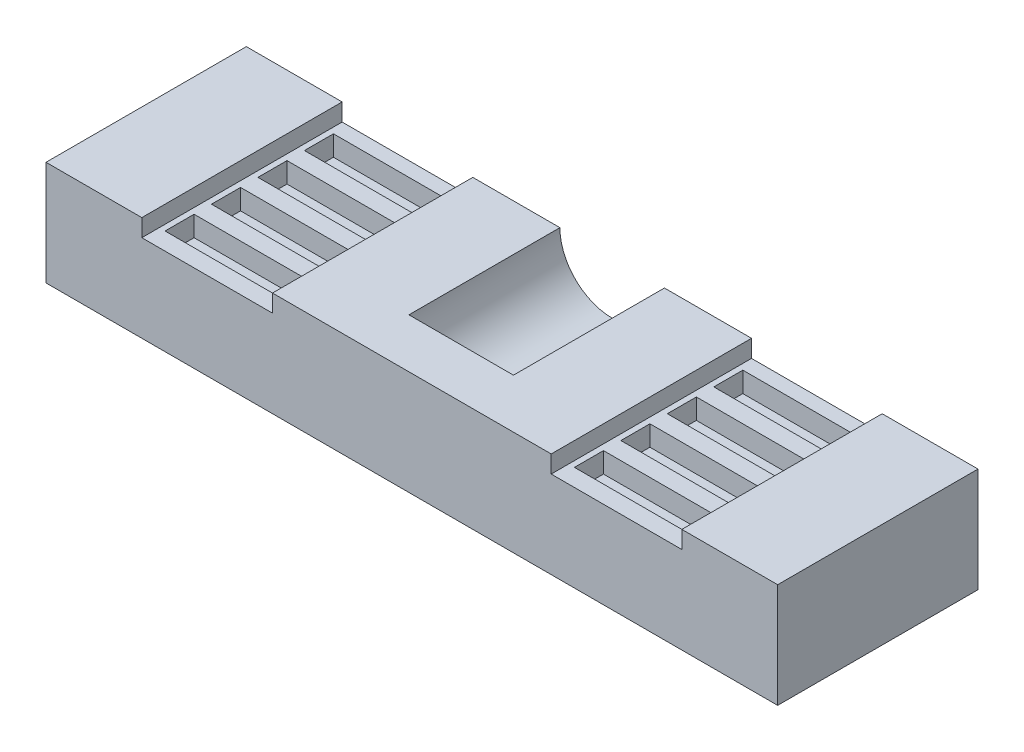
SolidWorks part; units mm, degrees
ref_plane "Alzado" through (0, 0, 0) normal (0, 0, 1) x (1, 0, 0)
ref_plane "Planta" through (0, 0, 0) normal (0, 1, 0) x (1, 0, 0)
ref_plane "Vista lateral" through (0, 0, 0) normal (1, 0, 0) x (0, 0, -1)
sketch "Croquis1" plane through (0, 0, 0) normal (0, 0, 1) x (1, 0, 0)
  line L0 (0, 0) -> (0, 18)
  line L1 (0, 18) -> (16.5, 18)
  line L2 (16.5, 18) -> (16.5, 15)
  line L3 (16.5, 15) -> (39, 15)
  line L4 (39, 15) -> (39, 18)
  line L5 (39, 18) -> (87, 18)
  line L6 (87, 18) -> (87, 15)
  line L7 (87, 15) -> (109.5, 15)
  line L8 (109.5, 15) -> (109.5, 18)
  line L9 (109.5, 18) -> (126, 18)
  line L10 (126, 18) -> (126, 0)
  line L11 (126, 0) -> (0, 0)
  dimension "D1" = 18
  dimension "D2" = 3
  dimension "D3" = 22.5
  dimension "D4" = 22.5
  dimension "D5" = 16.5
  dimension "D6" = 16.5
  dimension "D7" = 126
  dimension "D8" = 48
extrude "Saliente-Extruir1" add sketch "Croquis1" along normal blind 34.5
sketch "Croquis2" plane through (0, 0, 0) normal (0, 0, -1) x (-1, 0, 0)
  line L0 (-87, 18) -> (-39, 18) construction
  circle A0 centre (-63, 18) radius 9
extrude "Cortar-Extruir1" cut sketch "Croquis2" against normal blind 26
sketch "Croquis3" plane through (0, 15, 0) normal (0, 1, 0) x (1, 0, 0)
  line L0 (17.5, -31.5) -> (38, -31.5)
  line L1 (38, -31.5) -> (38, -26.5)
  line L2 (38, -26.5) -> (17.5, -26.5)
  line L3 (17.5, -26.5) -> (17.5, -31.5)
  line L4 (39, -34.5) -> (16.5, -34.5) construction
  line L5 (16.5, -34.5) -> (16.5, 0) construction
  line L7 (27.5, -31.5) -> (38, -31.5)
  line L9 (38, -26.5) -> (27.5, -26.5)
  line L11 (27.5, -23.5) -> (38, -23.5)
  line L13 (38, -18.5) -> (27.5, -18.5)
  line L15 (27.5, -15.5) -> (38, -15.5)
  line L17 (38, -10.5) -> (27.5, -10.5)
  line L19 (27.5, -7.5) -> (38, -7.5)
  line L21 (38, -2.5) -> (27.5, -2.5)
  line L22 (17.5, -18.5) -> (17.5, -23.5)
  line L23 (17.5, -23.5) -> (38, -23.5)
  line L24 (38, -23.5) -> (38, -18.5)
  line L25 (38, -18.5) -> (17.5, -18.5)
  line L26 (17.5, -10.5) -> (17.5, -15.5)
  line L27 (17.5, -15.5) -> (38, -15.5)
  line L28 (38, -15.5) -> (38, -10.5)
  line L29 (38, -10.5) -> (17.5, -10.5)
  line L30 (17.5, -2.5) -> (17.5, -7.5)
  line L31 (17.5, -7.5) -> (38, -7.5)
  line L32 (38, -7.5) -> (38, -2.5)
  line L33 (38, -2.5) -> (17.5, -2.5)
  line L34 (48, -7.5) -> (48, -2.5) [skipped]
  line L35 (48, -15.5) -> (48, -10.5) [skipped]
  line L36 (48, -23.5) -> (48, -18.5) [skipped]
  line L37 (48, -31.5) -> (48, -26.5) [skipped]
  line L38 (27.5, -26.5) -> (27.5, -31.5) [skipped]
  line L39 (27.5, -18.5) -> (27.5, -23.5) [skipped]
  line L40 (27.5, -10.5) -> (27.5, -15.5) [skipped]
  line L41 (27.5, -2.5) -> (27.5, -7.5) [skipped]
  line L43 (63, -34.5) -> (63, 2.3788) construction
  line L44 (87, -34.5) -> (39, -34.5) construction
  line L45 (88, -26.5) -> (108.5, -26.5)
  line L46 (88, -31.5) -> (88, -26.5)
  line L47 (108.5, -31.5) -> (88, -31.5)
  line L48 (108.5, -26.5) -> (108.5, -31.5)
  line L49 (88, -18.5) -> (108.5, -18.5)
  line L50 (88, -23.5) -> (88, -18.5)
  line L51 (108.5, -23.5) -> (88, -23.5)
  line L52 (108.5, -18.5) -> (108.5, -23.5)
  line L53 (88, -10.5) -> (108.5, -10.5)
  line L54 (88, -15.5) -> (88, -10.5)
  line L55 (108.5, -15.5) -> (88, -15.5)
  line L56 (108.5, -10.5) -> (108.5, -15.5)
  line L57 (88, -2.5) -> (108.5, -2.5)
  line L58 (88, -7.5) -> (88, -2.5)
  line L59 (108.5, -7.5) -> (88, -7.5)
  line L60 (108.5, -2.5) -> (108.5, -7.5)
  dimension "D1" = 20.5
  dimension "D2" = 5
  dimension "D3" = 3
  dimension "D4" = 1
  dimension "D5" = 4
  dimension "D6" = 2
extrude "Cortar-Extruir2" cut sketch "Croquis3" against normal blind 3.5 contours L2 L3 L0 L1 | L13 L25 L22 L23 L11 L24 | L17 L29 L26 L27 L15 L28 | L21 L33 L30 L31 L19 L32 | L48 L45 L46 L47 | L52 L49 L50 L51 | L56 L53 L54 L55 | L60 L57 L58 L59
